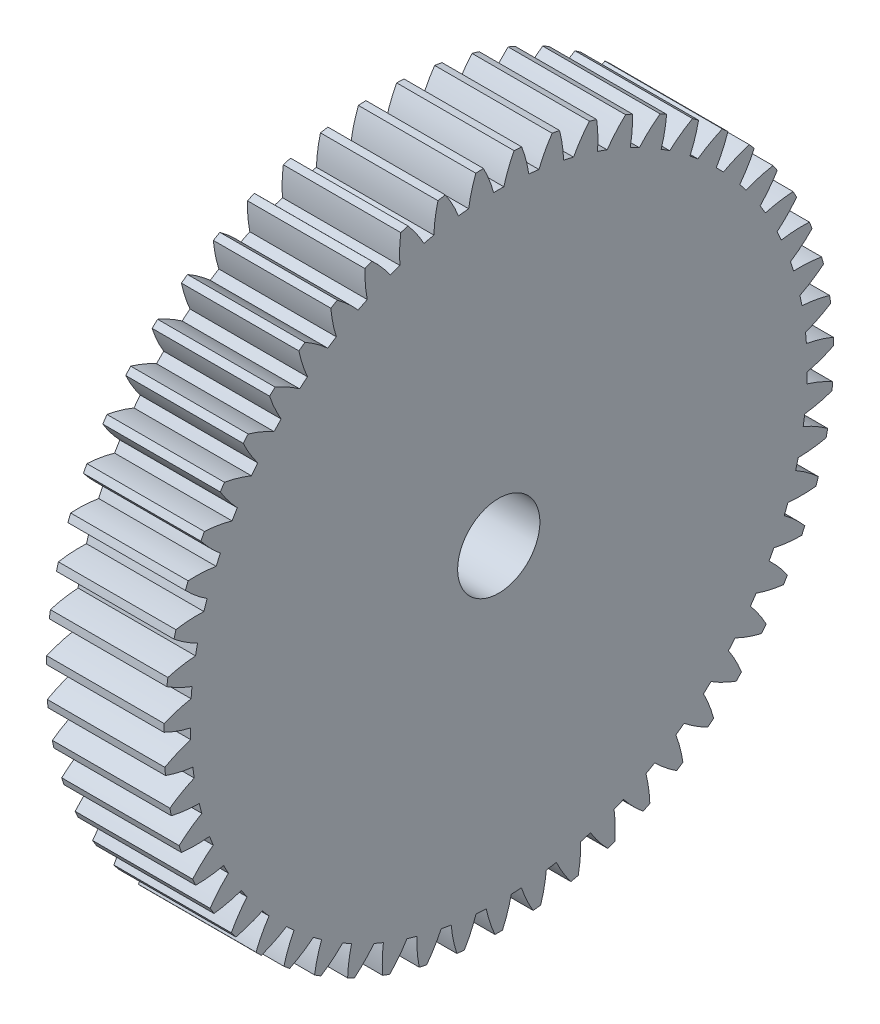
SolidWorks part; units mm, degrees
ref_plane "Plane1" through (0, 0, 0) normal (0, 0, 1) x (1, 0, 0)
ref_plane "Plane2" through (0, 0, 0) normal (0, 1, 0) x (1, 0, 0)
ref_plane "Plane3" through (0, 0, 0) normal (1, 0, 0) x (0, 0, -1)
sketch "HoldingSke" plane through (0, 0, 0) normal (0, 1, 0) x (1, 0, 0)
  line L0 (0, 0) -> (0.5736, -0.8192)
  line L1 (-15, 0) -> (100, 0) construction
  line L2 (0, 0) -> (-2.1039, 2.3779)
  line L3 (0, 0) -> (-11.863, 4.5341)
  line L4 (0, 0) -> (4.9534, 7.0742)
  line L5 (0, 0) -> (-46.8476, -17.4728)
  line L6 (0, 0) -> (-8.2896, -5.593)
  line L7 (-2.1039, 2.3779) -> (8.6586, 51.2059)
  line L8 (-76.2, 54.61) -> (-75.2, 54.61)
  line L9 (-71.009, 38.7566) -> (-53.1078, 45.2721)
  line L10 (-76.2, 71.12) -> (104.1128, 71.12)
  line L11 (0, 0) -> (-10, 0)
  line L12 (-76.2, 101.6) -> (-76.162, 101.6)
  line L13 (24.9733, 27.94) -> (52.9518, 28.4284)
  line L14 (24.9733, 27.94) -> (24.9743, 27.94)
  line L15 (24.9733, 27.94) -> (100.4006, 29.5858)
  line L16 (-63.627, -1) -> (-12.827, -1)
  circle A0 centre (0, 0) radius 3.5
  circle A1 centre (0, 0) radius 26.249
  circle A2 centre (0, 0) radius 37.5
  circle A3 centre (0, 0) radius 3.5
  dimension "MHD" = 52.498
  dimension "Hub_dia" = 75
  dimension "Bore" = 7
  dimension "MBD" = 7
  dimension "Num_teeth" = 55
  dimension "Pitch" = 1
  dimension "Overall_len" = 50
  dimension "Show_teeth" = 55
  dimension "Thickness" = 10
  dimension "OAL" = 50.0001
  dimension "T_dim" = 1
  dimension "Ap" = 20
  dimension "H" = 19.05
  dimension "Pitch_radius" = 180.3128
  dimension "Width" = 10
  dimension "Backlash" = 0.038
  dimension "Addendum_fac" = 1
  dimension "Dedendum_fac" = 1.25
  dimension "Clearance_fac" = 0.25
  dimension "Dedendum_add" = 0.001
  dimension "Module" = 1
sketch "BasProSke" plane through (0, 0, 0) normal (0, 1, 0) x (1, 0, 0)
  line L0 (-10, 0) -> (60, 0) construction
  line L1 (0, 0) -> (0, 28.5)
  line L2 (0, 0) -> (10, 0)
  line L3 (10, 0) -> (10, 28.5)
  line L4 (10, 28.5) -> (0, 28.5)
  dimension "Thickness" = 10
  dimension "Diameter" = 57
revolve "Base-Revolve" add sketch "BasProSke" angle 360 about L0
sketch "TooCutSke" plane through (0, 0, 0) normal (1, 0, 0) x (0, 0, -1)
  line L1 (0, 0) -> (0, 107) construction
  line L2 (0, 0) -> (-0.8518, 27.4868) construction
  line L3 (0, 0) -> (-3.1388, 54.8915) construction
  line L4 (-0.8518, 27.4868) -> (-1.5694, 27.4458) construction
  arc A0 (0.4336, 26.2454) -> (-0.4336, 26.2454) centre (0, 0) ccw
  arc A1 (1.3203, 28.4948) -> (-1.3203, 28.4948) centre (0, 0) ccw
  circle A2 centre (0, 0) radius 27.5 construction
  circle A3 centre (0, 0) radius 25.8415 construction
  arc A4 (-0.4336, 26.2454) -> (-1.3203, 28.4948) centre (-11.0486, 23.3605) ccw
  arc A5 (1.3203, 28.4948) -> (0.4336, 26.2454) centre (11.0486, 23.3605) ccw
  dimension "Root_dia" = 52.498
  dimension "Overcut_dia" = 57.0508
  dimension "Pitch_dia" = 55
  dimension "Base_dia" = 51.6831
  dimension "Flank_rad" = 11
  dimension "Half_ang" = 3.273
  dimension "Half_CT" = 0.7188
extrude "ToothCut" cut sketch "TooCutSke" along normal through all
fillet "Breaks" [suppressed] radius 0.02
fillet "RootFillets" [suppressed] radius 0.251
pattern_circular "TeethCuts" count 55 every 6.545 about axis through (-10, 0, 0) along (1, 0, 0) of "ToothCut", "RootFillets", "Breaks"
sketch "HubNeaOneSke" plane through (0, 0, 0) normal (-1, 0, 0) x (0, 0, 1)
  circle A0 centre (0, 0) radius 26.249
  dimension "Diameter" = 52.498
extrude "HubNearOne" [suppressed] add sketch "HubNeaOneSke" along normal blind 40.0001
sketch "HubNeaBotSke" plane through (0, 0, 0) normal (-1, 0, 0) x (0, 0, 1)
  circle A0 centre (0, 0) radius 26.249
  dimension "Diameter" = 52.498
extrude "HubNearBoth" [suppressed] add sketch "HubNeaBotSke" along normal blind 20
ref_plane "FarPln" through (10, 0, 0) normal (1, 0, 0) x (0, 0, -1)
sketch "HubFarSke" plane through (10, 0, 0) normal (1, 0, 0) x (0, 0, -1)
  circle A0 centre (0, 0) radius 26.249
  dimension "Diameter" = 52.498
extrude "HubFar" [suppressed] add sketch "HubFarSke" along normal blind 20
sketch "BorSke" plane through (0, 0, 0) normal (1, 0, 0) x (0, 0, -1)
  circle A0 centre (0, 0) radius 3.5
  dimension "Diameter" = 7
extrude "Bore" cut sketch "BorSke" along normal mid plane 100.0001
sketch "KeySke" plane through (0, 0, 0) normal (1, 0, 0) x (0, 0, -1)
  line L0 (-1, 0) -> (-1, 4.5)
  line L1 (-1, 4.5) -> (1, 4.5)
  line L2 (1, 4.5) -> (1, 0)
  line L3 (0, 0) -> (0, 34) construction
  line L4 (-1, 0) -> (1, 0)
  dimension "Offset" = 4.5
  dimension "Width" = 2
extrude "Keyway" [suppressed] cut sketch "KeySke" along normal mid plane 100.0001
pattern_circular "Keyway2" [suppressed] count 2 every 90 about axis through (-10, 0, 0) along (1, 0, 0)
equation "' \"Module@HoldingSke\" = 6.35"
equation "' \"Num_teeth@HoldingSke\" = 12"
equation "' \"Ap@HoldingSke\" =  20"
equation "' \"Ap@HoldingSke\" = 20"
equation "' \"Width@HoldingSke\" = 0.5 * 25.4"
equation "' \"Hub_dia@HoldingSke\"= 1 * 25.4"
equation "' \"Hub_dia@HoldingSke\" = 1 * 25.4"
equation "' \"Overall_len@HoldingSke\" = 1.0 * 25.4"
equation "' \"Bore@HoldingSke\" = 0.75 * 25.4"
equation "' \"T_dim@HoldingSke\" = 0.1 * 25.4"
equation "' \"Width@KeySke\" = 0.25 * 25.4"
equation "' \"Show_teeth@HoldingSke\" = 13"
equation "' \"Backlash@HoldingSke\" = 0.009 * 25.4"
equation "' \"Addendum_fac@HoldingSke\" = 1.0"
equation "' \"Dedendum_fac@HoldingSke\" = 1.25"
equation "' \"Dedendum_add@HoldingSke\" = 0.00005 * 25.4"
equation "' \"Clearance_fac@HoldingSke\" = 0.25"
equation "\"Pitch@HoldingSke\" = 1 / \"Module@HoldingSke\""
equation "\"Overcut_dia@TooCutSke\" = (\"Num_teeth@HoldingSke\" + 2 * \"Addendum_fac@HoldingSke\") / \"Pitch@HoldingSke\" + 0.002 * 25.4"
equation "\"Pitch_dia@TooCutSke\" = \"Num_teeth@HoldingSke\" / \"Pitch@HoldingSke\""
equation "\"Base_dia@TooCutSke\" = \"Num_teeth@HoldingSke\" / \"Pitch@HoldingSke\" * cos((\"Ap@HoldingSke\"  * 3.14159265 / 180))"
equation "\"Root_dia@TooCutSke\" = (\"Num_teeth@HoldingSke\" + 2) / \"Pitch@HoldingSke\" - 2 * (\"Addendum_fac@HoldingSke\" + \"Dedendum_fac@HoldingSke\") / \"Pitch@HoldingSke\" - \"Dedendum_add@HoldingSke\" * 2"
equation "\"Half_ang@TooCutSke\" = 180 / \"Num_teeth@HoldingSke\""
equation "\"Half_CT@TooCutSke\" = \"Num_teeth@HoldingSke\" / \"Pitch@HoldingSke\" * sin((3.14159265 / 2 / \"Num_teeth@HoldingSke\")) / 2 - 7 * \"Backlash@HoldingSke\" / 4"
equation "\"Flank_rad@TooCutSke\" = \"Num_teeth@HoldingSke\" / \"Pitch@HoldingSke\" / 5"
equation "\"Radius@RootFillets\" = \"Clearance_fac@HoldingSke\" / \"Pitch@HoldingSke\" + \"Dedendum_add@HoldingSke\""
equation "\"Break_rad@Breaks\" = 0.02 / \"Pitch@HoldingSke\""
equation "\"Thickness@HoldingSke\" = \"Width@HoldingSke\""
equation "\"OAL@HoldingSke\" = \"Thickness@HoldingSke\""
equation "\"MHD@HoldingSke\" = (\"Num_teeth@HoldingSke\" + 2) / \"Pitch@HoldingSke\" - 2 * (\"Addendum_fac@HoldingSke\" + \"Dedendum_fac@HoldingSke\")  / \"Pitch@HoldingSke\" - \"Dedendum_add@HoldingSke\" * 2"
equation "\"MBD@HoldingSke\" = (\"Num_teeth@HoldingSke\" + 2) / \"Pitch@HoldingSke\" - 2 * (\"Addendum_fac@HoldingSke\" + \"Dedendum_fac@HoldingSke\")  / \"Pitch@HoldingSke\" - \"Dedendum_add@HoldingSke\" * 2 - 0.002 * 25.4"
equation "\"MHD@HoldingSke\" = ((sgn( \"MHD@HoldingSke\" - \"Hub_dia@HoldingSke\" )-1)*( \"MHD@HoldingSke\" - \"Hub_dia@HoldingSke\" ))/-2+ \"Hub_dia@HoldingSke\""
equation "\"MBD@HoldingSke\" = ((sgn( \"MBD@HoldingSke\" - \"Bore@HoldingSke\" )-1)*( \"MBD@HoldingSke\" - \"Bore@HoldingSke\" ))/-2+ \"Bore@HoldingSke\""
equation "\"OAL@HoldingSke\" = ((sgn( \"OAL@HoldingSke\" - \"Overall_len@HoldingSke\" )+1)*( \"OAL@HoldingSke\" - \"Overall_len@HoldingSke\" ))/2 + \"Overall_len@HoldingSke\" + 0.000002 * 25.4"
equation "\"Num_teeth@TeethCuts\" = int( \"Show_teeth@HoldingSke\" ) + 1"
equation "\"Num_teeth@TeethCuts\" = ((sgn( \"Num_teeth@TeethCuts\" - \"Num_teeth@HoldingSke\" )-1)*( \"Num_teeth@TeethCuts\" - \"Num_teeth@HoldingSke\" ))/-2+ \"Num_teeth@HoldingSke\""
equation "\"Num_teeth@TeethCuts\" = ((sgn( \"Num_teeth@TeethCuts\" - 2.0)+1)*( \"Num_teeth@TeethCuts\" - 2.0))/2 +2.0"
equation "\"Angle@TeethCuts\" = 360.0 / \"Num_teeth@HoldingSke\""
equation "\"Diameter@BasProSke\" = (\"Num_teeth@HoldingSke\" + 2 * \"Addendum_fac@HoldingSke\") / \"Pitch@HoldingSke\""
equation "\"Thickness@BasProSke\"  = \"Thickness@HoldingSke\""
equation "' \"Fillet_rad@BasProSke\" =  \"Thickness@HoldingSke\" * 0.05"
equation "' \"Fillet_rad@BasProSke\" = \"Thickness@HoldingSke\" * 0.05"
equation "\"MHD@HoldingSke\" = ((sgn( \"MHD@HoldingSke\" - \"Root_dia@TooCutSke\" )-1)*( \"MHD@HoldingSke\" - \"Root_dia@TooCutSke\" ))/-2+ \"Root_dia@TooCutSke\""
equation "\"Diameter@HubNeaOneSke\" = \"MHD@HoldingSke\""
equation "\"Length@HubNearOne\" = \"OAL@HoldingSke\" - \"Thickness@BasProSke\""
equation "\"Diameter@HubNeaBotSke\" = \"MHD@HoldingSke\""
equation "\"Length@HubNearBoth\" = ( \"OAL@HoldingSke\" - \"Thickness@BasProSke\" ) / 2.0"
equation "\"Thickness@FarPln\" = \"Thickness@BasProSke\""
equation "\"Diameter@HubFarSke\" = \"MHD@HoldingSke\""
equation "\"Length@HubFar\" = ( \"OAL@HoldingSke\" - \"Thickness@BasProSke\" ) / 2.0"
equation "\"Diameter@BorSke\" = \"MBD@HoldingSke\""
equation "\"D1@Bore\" = \"OAL@HoldingSke\" * 2.0"
equation "\"D1@Keyway\" = \"OAL@HoldingSke\" * 2.0"
equation "\"Offset@KeySke\" = \"T_dim@HoldingSke\" + \"MBD@HoldingSke\" / 2.0"
